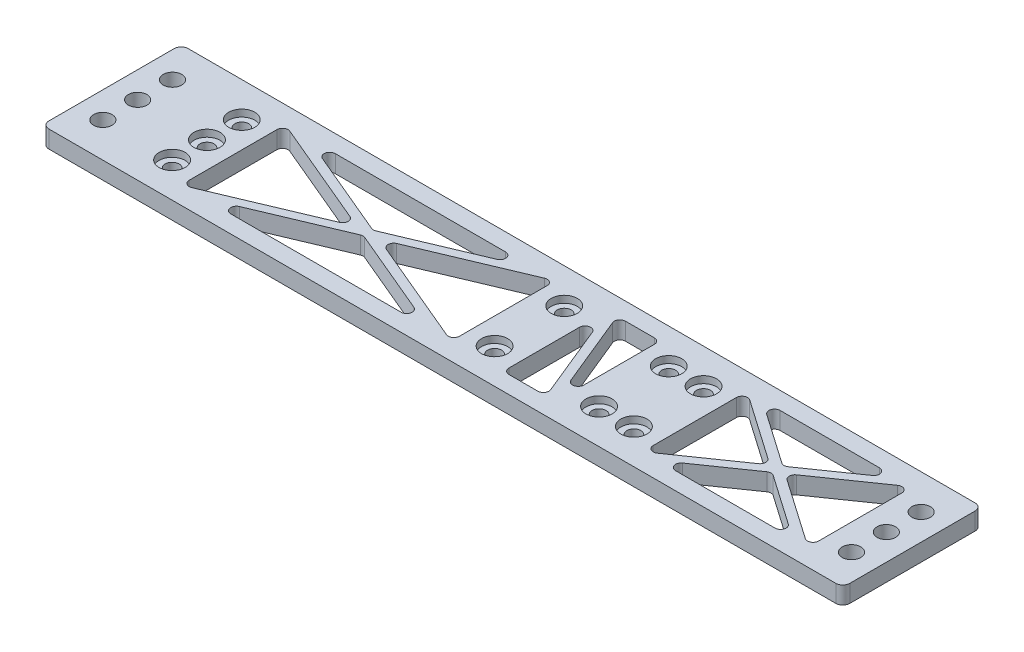
SolidWorks part; units mm, degrees
material "6061-T6 (SS)"
ref_plane "Front" through (0, 0, 0) normal (0, 0, 1) x (1, 0, 0)
ref_plane "Top" through (0, 0, 0) normal (0, 1, 0) x (1, 0, 0)
ref_plane "Right" through (0, 0, 0) normal (1, 0, 0) x (0, 0, -1)
sketch "Sketch1" plane through (0, 0, 0) normal (0, 1, 0) x (1, 0, 0)
  line L1 (-146.05, -25.4) -> (146.05, -25.4)
  line L2 (-146.05, -25.4) -> (-146.05, 25.4)
  line L3 (-146.05, 25.4) -> (146.05, 25.4)
  line L4 (146.05, -25.4) -> (146.05, 25.4)
  line L5 (-146.05, -25.4) -> (146.05, 25.4) construction
  line L6 (-146.05, 25.4) -> (146.05, -25.4) construction
  point P0 (0, 0)
  dimension "D1" = 50.8
  dimension "D2" = 292.1
extrude "Boss-Extrude1" add sketch "Sketch1" along normal blind 6.35
sketch "Sketch4" plane through (0, 6.35, 0) normal (0, 1, 0) x (1, 0, 0)
  line L0 (146.05, -25.4) -> (146.05, 25.4) construction
  line L1 (6.35, -12.7) -> (6.35, 12.7) construction
  line L2 (-146.05, 25.4) -> (-146.05, -25.4) construction
  line L3 (-111.252, 25.4) -> (-111.252, 12.7) construction
  line L4 (146.05, 25.4) -> (-146.05, 25.4) construction
  line L5 (-111.252, 12.7) -> (-111.252, 0) construction
  line L6 (-111.252, 0) -> (-111.252, -12.7) construction
  line L7 (-111.252, -12.7) -> (-111.252, -25.4) construction
  line L8 (-146.05, -25.4) -> (146.05, -25.4) construction
  point P0 (44.45, 12.7)
  point P2 (6.35, 12.7)
  point P4 (6.35, -12.7)
  point P6 (44.45, -12.7)
  point P23 (6.35, 0)
  point P25 (-111.252, 12.7)
  point P27 (-111.252, 0)
  point P29 (-111.252, -12.7)
  point P47 (57.15, 12.7)
  point P49 (57.15, -12.7)
  dimension "D1" = 38.1
  dimension "D2" = 101.6
  dimension "D3" = 25.4
  dimension "D4" = 34.798
  dimension "D5" = 12.7
hole_wizard "CBORE for #10 Socket Head Cap Screw1" positions "Sketch4" profile "Sketch3" counterbore size "#10" standard "ANSI Inch" end condition through all
sketch "Sketch3" plane through (44.45, 6.35, -12.7) normal (1, 0, 0) x (0, 0, 1)
  line L0 (0, 0) -> (0, 6.35)
  line L1 (0, 6.35) -> (2.5527, 6.35)
  line L3 (2.5527, 6.35) -> (2.5527, 2.54)
  line L4 (2.5527, 2.54) -> (4.7625, 2.54)
  line L5 (4.7625, 2.54) -> (4.7625, 0)
  line L7 (4.7625, 0) -> (0, 0)
  line L11 (0, -6.35) -> (0, 107.95) construction
  dimension "Thru Hole Dia." = 5.1054
  dimension "Thru Hole Depth" = 6.35
  dimension "C'Bore Dia." = 9.525
  dimension "C'Bore Depth" = 2.54
sketch "Sketch7" plane through (0, 0, 0) normal (0, -1, 0) x (1, 0, 0)
  line L5 (-136.525, 25.4) -> (-136.525, 12.7) construction
  line L6 (-146.05, 25.4) -> (146.05, 25.4) construction
  line L7 (-136.525, 12.7) -> (-136.525, 0) construction
  line L8 (-136.525, 0) -> (-136.525, -12.7) construction
  line L9 (-136.525, -12.7) -> (-136.525, -25.4) construction
  line L10 (146.05, -25.4) -> (-146.05, -25.4) construction
  line L12 (-146.05, -25.4) -> (-146.05, 25.4) construction
  line L13 (146.05, 25.4) -> (146.05, -25.4) construction
  point P0 (-136.525, 12.7)
  point P2 (-136.525, 0)
  point P4 (-136.525, -12.7)
  point P6 (136.525, 12.7)
  point P8 (136.525, 0)
  point P10 (136.525, -12.7)
  dimension "D1" = 9.525
  dimension "D2" = 9.525
hole_wizard "1/4 Clearance Hole1" positions "Sketch7" profile "Sketch6" hole size "1/4" standard "ANSI Inch" end condition through all
sketch "Sketch6" plane through (-136.525, 0, 12.7) normal (1, 0, 0) x (0, 0, -1)
  line L0 (0, 0) -> (0, 6.35)
  line L1 (0, 6.35) -> (3.3782, 6.35)
  line L2 (3.3782, 6.35) -> (3.3782, 0)
  line L5 (3.3782, 0) -> (0, 0)
  line L11 (0, -6.35) -> (0, 107.95) construction
  dimension "Thru Hole Dia." = 6.7564
  dimension "Thru Hole Depth" = 6.35
fillet "Fillet1" radius 2.54 4 edges at (146.05, 3.175, -25.4) (146.05, 3.175, 25.4) (-146.05, 3.175, 25.4) (-146.05, 3.175, -25.4)
sketch "Sketch8" plane through (0, 0, 0) normal (0, -1, 0) x (1, 0, 0)
  line L3 (143.51, -25.4) -> (-143.51, -25.4) construction
  line L4 (-83.5024, -19.05) -> (-21.3996, -19.05)
  line L5 (-101.727, -15.9882) -> (-101.727, 15.9882)
  line L6 (-83.5024, 19.05) -> (-21.3996, 19.05)
  line L7 (-3.175, -15.9882) -> (-3.175, 15.9882)
  line L8 (-143.51, 25.4) -> (143.51, 25.4) construction
  line L9 (-84.2917, -15.1456) -> (-53.2403, -2.0555)
  line L10 (-20.6103, 15.1456) -> (-51.6617, 2.0555)
  line L11 (-20.6103, -15.1456) -> (-51.6617, -2.0555)
  line L12 (-84.2917, 15.1456) -> (-53.2403, 2.0555)
  line L13 (-43.9226, 1.8724) -> (-5.9963, 17.8606)
  line L14 (-43.9226, -1.8724) -> (-5.9963, -17.8606)
  line L15 (-60.9794, -1.8724) -> (-98.9057, -17.8606)
  line L16 (-60.9794, 1.8724) -> (-98.9057, 17.8606)
  line L17 (-68.766, -8.6006) -> (-69.9994, -5.6749) construction
  line L18 (-36.136, -8.6006) -> (-34.9026, -5.6749) construction
  line L19 (20.4554, -16.2473) -> (31.0128, 9.5067)
  line L20 (22.3355, -19.05) -> (32.893, -19.05)
  line L21 (15.875, -8.7359) -> (15.875, 17.018)
  line L22 (17.907, 19.05) -> (28.4645, 19.05)
  line L23 (34.925, -17.018) -> (34.925, 8.7359)
  line L24 (78.7135, -19.05) -> (114.9615, -19.05)
  line L25 (66.675, -15.161) -> (66.675, 15.161)
  line L26 (78.7135, 19.05) -> (114.9615, 19.05)
  line L27 (127, -15.161) -> (127, 15.161)
  line L28 (30.3446, 16.2473) -> (19.7872, -9.5067)
  line L29 (77.5531, -15.35) -> (95.677, -2.7412)
  line L30 (116.1219, 15.35) -> (97.998, 2.7412)
  line L31 (116.1219, -15.35) -> (97.998, -2.7412)
  line L32 (77.5531, 15.35) -> (95.677, 2.7412)
  line L33 (91.66, 1.668) -> (69.8675, 16.829)
  line L34 (102.015, 1.668) -> (123.8075, 16.829)
  line L35 (102.015, -1.668) -> (123.8075, -16.829)
  line L36 (91.66, -1.668) -> (69.8675, -16.829)
  line L37 (80.7637, 9.2485) -> (82.577, 11.8549) construction
  line L38 (112.9113, 9.2485) -> (111.098, 11.8549) construction
  circle A0 centre (-111.252, -12.7) radius 4.7625 construction
  circle A1 centre (6.35, -12.7) radius 4.7625 construction
  arc A2 (-101.727, -15.9882) -> (-98.9057, -17.8606) centre (-99.695, -15.9882) ccw
  arc A3 (-98.9057, 17.8606) -> (-101.727, 15.9882) centre (-99.695, 15.9882) ccw
  arc A4 (-83.5024, 19.05) -> (-84.2917, 15.1456) centre (-83.5024, 17.018) ccw
  arc A5 (-60.9794, -1.8724) -> (-60.9794, 1.8724) centre (-61.7687, 0) ccw
  arc A6 (-53.2403, 2.0555) -> (-51.6617, 2.0555) centre (-52.451, 3.928) ccw
  arc A7 (-53.2403, -2.0555) -> (-51.6617, -2.0555) centre (-52.451, -3.928) cw
  arc A8 (-43.9226, 1.8724) -> (-43.9226, -1.8724) centre (-43.1333, 0) ccw
  arc A9 (-20.6103, 15.1456) -> (-21.3996, 19.05) centre (-21.3996, 17.018) ccw
  arc A10 (-3.175, 15.9882) -> (-5.9963, 17.8606) centre (-5.207, 15.9882) ccw
  arc A11 (-5.9963, -17.8606) -> (-3.175, -15.9882) centre (-5.207, -15.9882) ccw
  arc A12 (-21.3996, -19.05) -> (-20.6103, -15.1456) centre (-21.3996, -17.018) ccw
  arc A13 (-83.5024, -19.05) -> (-84.2917, -15.1456) centre (-83.5024, -17.018) cw
  circle A14 centre (44.45, -12.7) radius 4.7625 construction
  circle A15 centre (136.525, -12.7) radius 3.3782 construction
  circle A16 centre (57.15, -12.7) radius 4.7625 construction
  arc A17 (32.893, -19.05) -> (34.925, -17.018) centre (32.893, -17.018) ccw
  arc A18 (31.0128, 9.5067) -> (34.925, 8.7359) centre (32.893, 8.7359) cw
  arc A19 (30.3446, 16.2473) -> (28.4645, 19.05) centre (28.4645, 17.018) ccw
  arc A20 (15.875, 17.018) -> (17.907, 19.05) centre (17.907, 17.018) cw
  arc A21 (15.875, -8.7359) -> (19.7872, -9.5067) centre (17.907, -8.7359) ccw
  arc A22 (20.4554, -16.2473) -> (22.3355, -19.05) centre (22.3355, -17.018) ccw
  arc A23 (97.998, -2.7412) -> (95.677, -2.7412) centre (96.8375, -4.4092) ccw
  arc A24 (114.9615, -19.05) -> (116.1219, -15.35) centre (114.9615, -17.018) ccw
  arc A25 (123.8075, -16.829) -> (127, -15.161) centre (124.968, -15.161) ccw
  arc A26 (123.8075, 16.829) -> (127, 15.161) centre (124.968, 15.161) cw
  arc A27 (102.015, 1.668) -> (102.015, -1.668) centre (103.1754, 0) ccw
  arc A28 (114.9615, 19.05) -> (116.1219, 15.35) centre (114.9615, 17.018) cw
  arc A29 (77.5531, 15.35) -> (78.7135, 19.05) centre (78.7135, 17.018) cw
  arc A30 (95.677, 2.7412) -> (97.998, 2.7412) centre (96.8375, 4.4092) ccw
  arc A31 (91.66, 1.668) -> (91.66, -1.668) centre (90.4996, 0) cw
  arc A32 (66.675, 15.161) -> (69.8675, 16.829) centre (68.707, 15.161) cw
  arc A33 (66.675, -15.161) -> (69.8675, -16.829) centre (68.707, -15.161) ccw
  arc A34 (77.5531, -15.35) -> (78.7135, -19.05) centre (78.7135, -17.018) ccw
  point P30 (-56.5377, 0)
  point P37 (-48.3643, 0)
  point P49 (-101.727, -19.05)
  point P50 (-101.727, 19.05)
  point P81 (15.875, -19.05)
  point P93 (0, 0)
  point P105 (99.6173, 0)
  point P114 (94.0577, 0)
  point P123 (66.675, -19.05)
  dimension "D7" = 2.032
  dimension "D13" = 2.032
  dimension "D15" = 2.032
  dimension "D1" = 6.35
  dimension "D2" = 6.35
  dimension "D3" = 9.525
  dimension "D4" = 9.525
  dimension "D5" = 9.525
  dimension "D6" = 3.175
  dimension "D8" = 38.1
  dimension "D9" = 9.525
  dimension "D10" = 9.525
  dimension "D11" = 9.525
  dimension "D12" = 3.175
  dimension "D14" = 3.175
extrude "Cut-Extrude1" cut sketch "Sketch8" against normal through all
